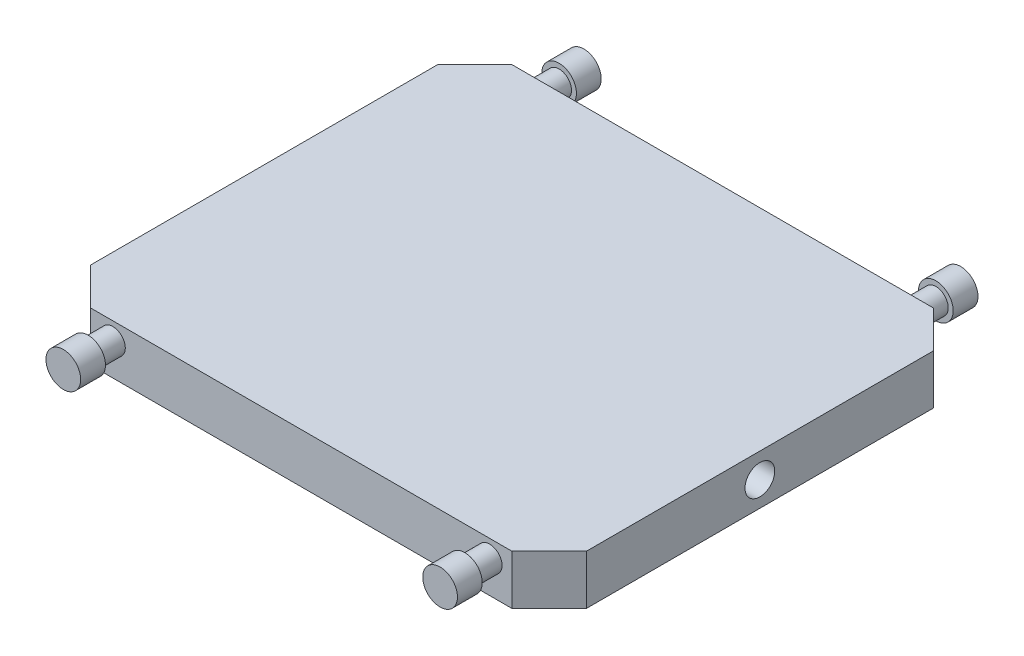
SolidWorks part; units mm, degrees
ref_plane "Front Plane" through (0, 0, 0) normal (0, 0, 1) x (1, 0, 0)
ref_plane "Top Plane" through (0, 0, 0) normal (0, 1, 0) x (1, 0, 0)
ref_plane "Right Plane" through (0, 0, 0) normal (1, 0, 0) x (0, 0, -1)
sketch "Sketch1" plane through (0, 0, 0) normal (0, 1, 0) x (1, 0, 0)
  line L0 (0, 310) -> (30, 340)
  line L1 (30, 0) -> (370, 0)
  line L2 (0, 30) -> (0, 310)
  line L3 (30, 340) -> (370, 340)
  line L4 (400, 30) -> (400, 310)
  line L5 (0, 30) -> (30, 0)
  line L6 (370, 0) -> (400, 30)
  line L7 (370, 340) -> (400, 310)
  point P0 (0, 0)
  point P1 (400, 340)
  point P2 (0, 340)
  point P3 (400, 0)
  dimension "D1" = 340
  dimension "D2" = 400
extrude "Boss-Extrude1" add sketch "Sketch1" along normal blind 40
sketch "Sketch2" plane through (0, 0, 0) normal (-1, 0, 0) x (0, 0, 1)
  line L0 (-310, 40) -> (-30, 40) construction
  circle A0 centre (-170, 20) radius 12
  point P2 (0, 0)
  point P5 (-170, 40)
  dimension "D1" = 24
extrude "Cut-Extrude1" cut sketch "Sketch2" against normal through all
sketch "Sketch3" plane through (0, 0, 0) normal (0, 0, 1) x (1, 0, 0)
  line L0 (30, 40) -> (370, 40) construction
  line L1 (30, 40) -> (30, 0) construction
  line L2 (200, 55.1918) -> (200, -40.6233) construction
  circle A0 centre (48, 26) radius 10
  circle A1 centre (352, 26) radius 10
  dimension "D1" = 20
  dimension "D2" = 14
  dimension "D3" = 18
extrude "Boss-Extrude2" add sketch "Sketch3" along normal blind 20
sketch "Sketch4" plane through (0, 0, 20) normal (0, 0, 1) x (1, 0, 0)
  circle A0 centre (48, 26) radius 14
  circle A1 centre (352, 26) radius 14
extrude "Boss-Extrude3" add sketch "Sketch4" along normal blind 20
ref_plane "Plane1" through (0, 0, -170) normal (0, 0, 1) x (1, 0, 0)
mirror "Mirror1" about plane through (0, 0, -170) normal (0, 0, 1) of "Boss-Extrude3", "Boss-Extrude2"
